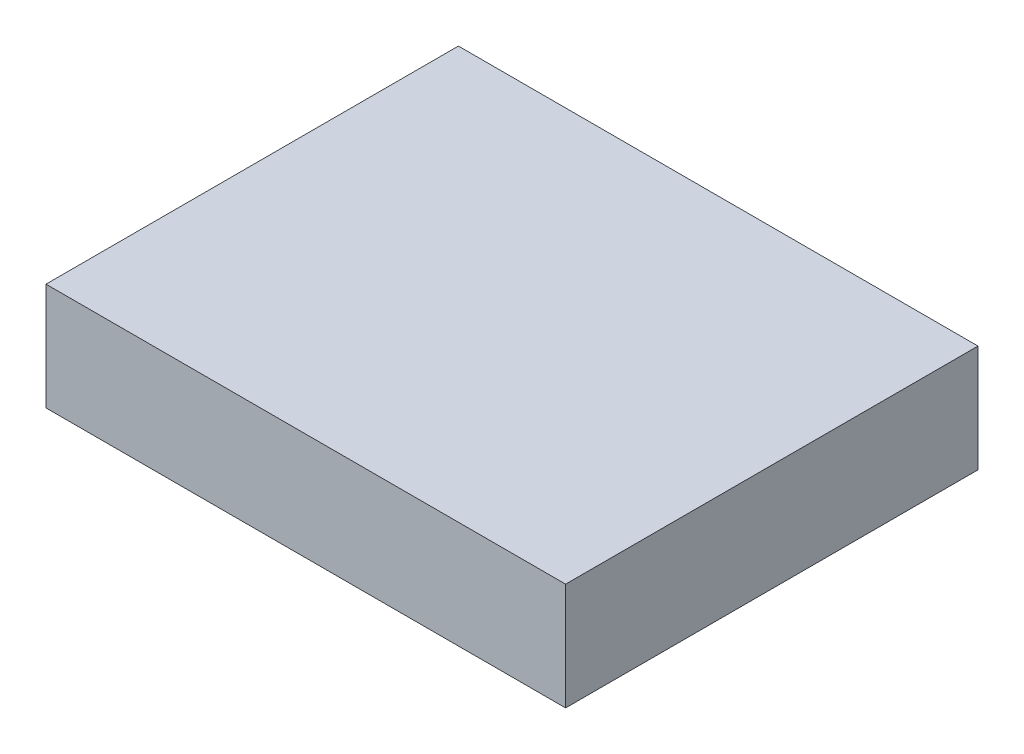
SolidWorks part; units mm, degrees
ref_plane "Front Plane" through (0, 0, 0) normal (0, 0, 1) x (1, 0, 0)
ref_plane "Top Plane" through (0, 0, 0) normal (0, 1, 0) x (1, 0, 0)
ref_plane "Right Plane" through (0, 0, 0) normal (1, 0, 0) x (0, 0, -1)
sketch "Sketch2" plane through (0, 0, 0) normal (0, 1, 0) x (1, 0, 0)
  line L1 (-80.01, 63.5) -> (80.01, 63.5)
  line L2 (-80.01, 63.5) -> (-80.01, -63.5)
  line L3 (-80.01, -63.5) -> (80.01, -63.5)
  line L4 (80.01, 63.5) -> (80.01, -63.5)
  line L5 (-80.01, 63.5) -> (80.01, -63.5) construction
  line L6 (-80.01, -63.5) -> (80.01, 63.5) construction
  point P0 (0, 0)
  dimension "D1" = 160.02
  dimension "D2" = 127
extrude "Boss-Extrude2" add sketch "Sketch2" along normal blind 33.02 contours L2 L3 L4 L1
sketch "Sketch6" plane through (0, 0, -63.5) normal (0, 0, -1) x (-1, 0, 0)
  line L0 (-80.01, 16.51) -> (80.01, 16.51) construction
  line L1 (-80.01, 33.02) -> (-80.01, 0) construction
  line L2 (80.01, 33.02) -> (80.01, 0) construction
  line L3 (0, 16.51) -> (0, 1.2424) construction
  line L4 (0, 1.2424) -> (19.1821, 27.1441) construction
  line L5 (0, 16.51) -> (0, 33.02) construction
  line L6 (80.01, 33.02) -> (-80.01, 33.02) construction
  line L7 (-37.592, 9.525) -> (-52.0352, 9.525) construction
  line L8 (-37.592, 9.525) -> (37.592, 9.525)
  line L9 (-37.592, 9.525) -> (-37.592, 23.495)
  line L10 (-37.592, 23.495) -> (37.592, 23.495)
  line L11 (37.592, 9.525) -> (37.592, 23.495)
  line L12 (-37.592, 9.525) -> (37.592, 23.495) construction
  line L13 (-37.592, 23.495) -> (37.592, 9.525) construction
  line L14 (-48.768, 9.525) -> (-40.132, 9.525)
  line L15 (-48.768, 9.525) -> (-48.768, 20.955)
  line L16 (-40.132, 9.525) -> (-40.132, 20.955)
  line L17 (-48.768, 20.955) -> (-40.132, 20.955)
  circle A0 centre (-56.5912, 16.51) radius 6.35
  circle A1 centre (56.5912, 16.51) radius 6.35
  point P21 (-44.8102, 16.51)
  dimension "D1" = 13.97
  dimension "D2" = 12.7
  dimension "D3" = 23.4188
  dimension "D4" = 75.184
  dimension "D5" = 11.43
  dimension "D6" = 8.636
  dimension "D7" = 2.54
